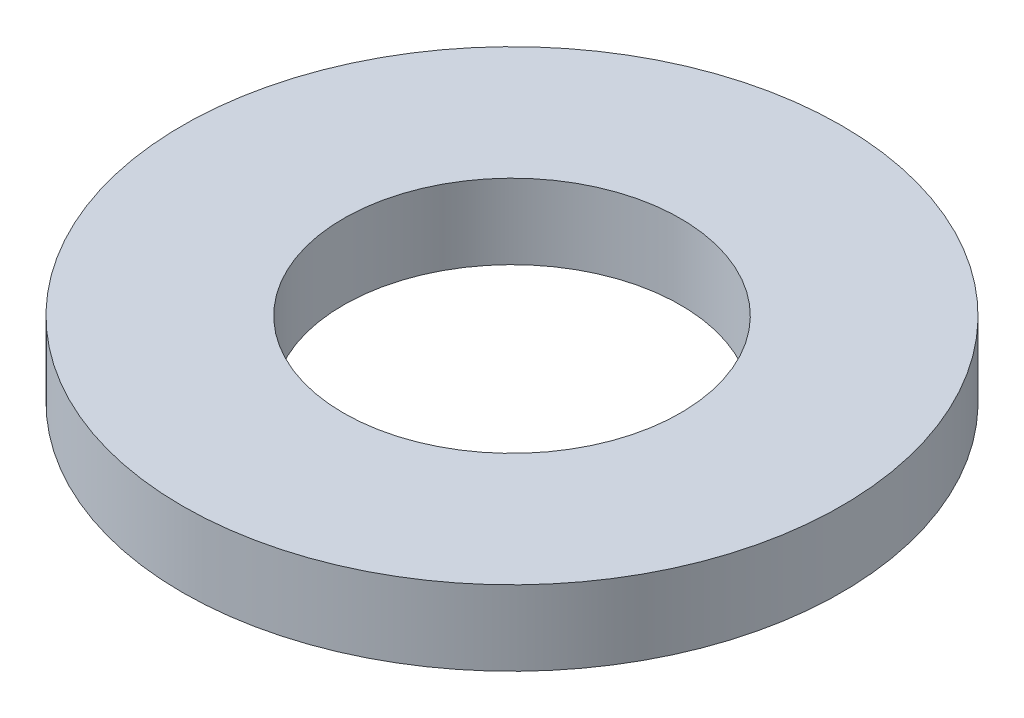
SolidWorks part; units mm, degrees
material "ABS"
ref_plane "前视基准面" through (0, 0, 0) normal (0, 0, 1) x (1, 0, 0)
ref_plane "上视基准面" through (0, 0, 0) normal (0, 1, 0) x (1, 0, 0)
ref_plane "右视基准面" through (0, 0, 0) normal (1, 0, 0) x (0, 0, -1)
sketch "草图1" plane through (0, 0, 0) normal (0, 1, 0) x (1, 0, 0)
  circle A0 centre (0, 0) radius 2.25
  circle A1 centre (0, 0) radius 4.4
  dimension "D1" = 4.5
  dimension "D2" = 8.8
extrude "凸台-拉伸1" add sketch "草图1" along normal blind 1
